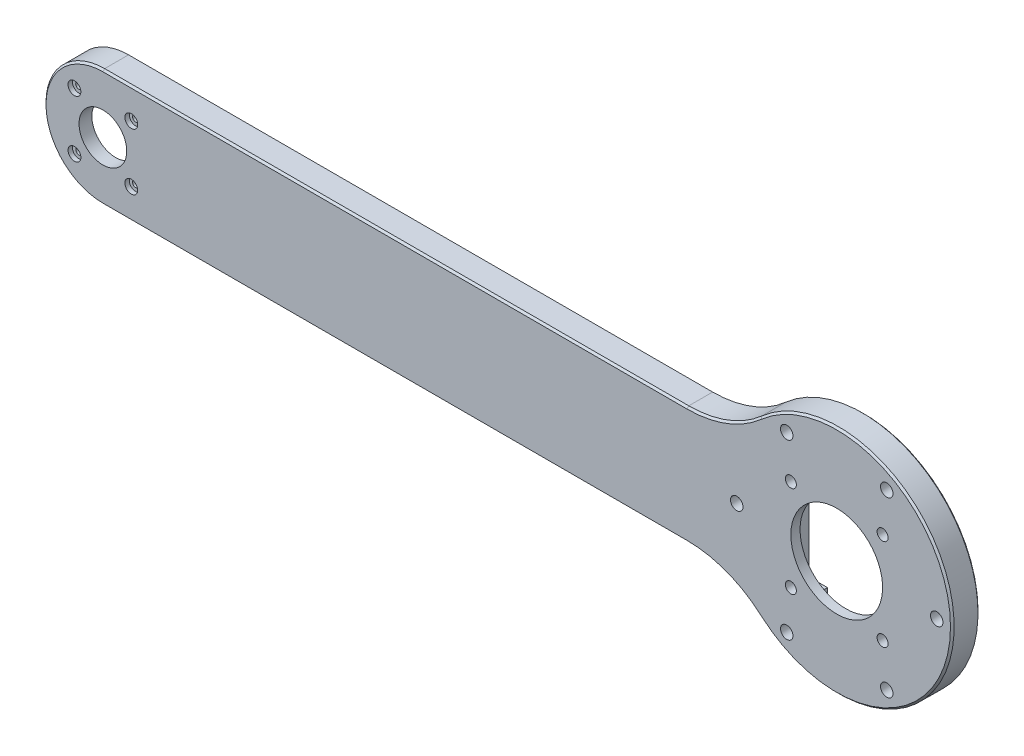
SolidWorks part; units mm, degrees
ref_plane "前基準面" through (0, 0, 0) normal (0, 0, 1) x (1, 0, 0)
ref_plane "上基準面" through (0, 0, 0) normal (0, 1, 0) x (1, 0, 0)
ref_plane "右基準面" through (0, 0, 0) normal (1, 0, 0) x (0, 0, -1)
sketch "Sketch1" plane through (0, 0, 0) normal (0, 0, 1) x (1, 0, 0)
  line L0 (393.8323, -17.9415) -> (-6.1677, -17.9415) construction
  line L1 (393.8323, 45.0585) -> (-6.1677, 45.0585)
  line L2 (393.8323, -80.9415) -> (-6.1677, -80.9415)
  line L3 (-6.1677, 14.0585) -> (339.5645, 14.0585)
  line L4 (-6.1677, -49.9415) -> (339.5645, -49.9415)
  line L6 (423.8323, -47.9415) -> (363.8323, -47.9415)
  line L7 (423.8323, -47.9415) -> (423.8323, 12.0585)
  line L8 (423.8323, 12.0585) -> (363.8323, 12.0585)
  line L9 (363.8323, -47.9415) -> (363.8323, 12.0585)
  line L10 (393.8323, 12.0585) -> (393.8323, -47.9415) construction
  line L11 (423.8323, -17.9415) -> (363.8323, -17.9415) construction
  line L12 (413.8323, -47.9415) -> (373.8323, -47.9415)
  line L13 (413.8323, -47.9415) -> (413.8323, -80.9415)
  line L14 (413.8323, -80.9415) -> (373.8323, -80.9415)
  line L15 (373.8323, -47.9415) -> (373.8323, -80.9415)
  arc A0 (393.8323, 45.0585) -> (393.8323, -80.9415) centre (393.8323, -17.9415) cw
  arc A1 (-6.1677, 45.0585) -> (-6.1677, -80.9415) centre (-6.1677, -17.9415) ccw
  circle A4 centre (-6.1677, -17.9415) radius 32
  circle A5 centre (393.8323, -17.9415) radius 63
  circle A6 centre (393.8323, -17.9415) radius 25 construction
  circle A7 centre (393.8323, -17.9415) radius 25
  arc A8 (435.6431, -47.1452) -> (352.0215, -47.1452) centre (393.8323, -17.9415) ccw construction
  dimension "D1" = 400
  dimension "D2" = 60
  dimension "D4" = 60
  dimension "D5" = 10
  dimension "D6" = 12
  dimension "D3" = 64
sketch "Sketch2" plane through (0, 0, 0) normal (0, 0, 1) x (1, 0, 0)
  line L0 (-6.1677, -49.9415) -> (339.5645, -49.9415) construction
  line L1 (-6.1677, 14.0585) -> (339.5645, 14.0585) construction
  line L2 (-6.1677, -49.9415) -> (339.5645, -49.9415)
  line L3 (-6.1677, 14.0585) -> (339.5645, 14.0585)
  circle A0 centre (-6.1677, -17.9415) radius 32 construction
  arc A2 (-6.1677, 14.0585) -> (-6.1677, -49.9415) centre (-6.1677, -17.9415) ccw
  circle A5 centre (393.8323, -17.9415) radius 63 construction
  arc A6 (339.5645, -49.9415) -> (339.5645, 14.0585) centre (393.8323, -17.9415) ccw
extrude "Boss-Extrude1" add sketch "Sketch2" along normal blind 15
fillet "Fillet1" radius 60 2 edges at (339.5645, 14.0585, 7.5) (339.5645, -49.9415, 7.5)
ref_plane "平面1" through (0, 0, 10) normal (0, 0, 1) x (1, 0, 0)
sketch "Sketch9" plane through (0, 0, 15) normal (0, 0, 1) x (1, 0, 0)
  line L0 (330.8323, -17.9415) -> (25.8323, -17.9415) construction
  line L1 (165.3718, 9.0585) -> (165.3718, -44.9415) construction
  line L2 (393.8323, -17.9415) -> (263.8323, 9.0585) construction
  line L3 (312.1929, 14.0585) -> (-6.1677, 14.0585) construction
  line L4 (336.9113, 9.0585) -> (-6.1677, 9.0585)
  line L6 (-6.1677, -44.9415) -> (312.1929, -44.9415)
  line L7 (-6.1677, -44.9415) -> (336.9113, -44.9415)
  circle A0 centre (393.8323, -17.9415) radius 63
  arc A1 (352.017, -65.0635) -> (352.017, 29.1804) centre (393.8323, -17.9415) ccw construction
  circle A2 centre (-6.1677, -17.9415) radius 32
  arc A3 (-6.1677, 14.0585) -> (-6.1677, -49.9415) centre (-6.1677, -17.9415) ccw construction
  dimension "D3" = 130
  dimension "D1" = 5
  dimension "D2" = 5
sketch "Sketch10" plane through (0, 0, 15) normal (0, 0, 1) x (1, 0, 0)
  line L0 (336.9113, 9.0585) -> (-6.1677, 9.0585) construction
  line L1 (-6.1677, -44.9415) -> (336.9113, -44.9415) construction
  line L2 (336.9113, 9.0585) -> (11.0079, 9.0585)
  line L3 (11.0079, -44.9415) -> (336.9113, -44.9415)
  circle A0 centre (393.8323, -17.9415) radius 63 construction
  circle A1 centre (-6.1677, -17.9415) radius 32 construction
  arc A2 (336.9113, 9.0585) -> (336.9113, -44.9415) centre (393.8323, -17.9415) ccw
  arc A3 (11.0079, -44.9415) -> (11.0079, 9.0585) centre (-6.1677, -17.9415) ccw
extrude "Cut-Extrude4" [suppressed] cut sketch "Sketch10" against normal offset from surface (12 mm away) 3
sketch "草圖2" plane through (0, 0, 0) normal (0, 0, -1) x (-1, 0, 0)
  circle A0 centre (-393.8323, -17.9415) radius 25 construction
  circle A1 centre (-393.8323, -17.9415) radius 25
extrude "除料-伸長2" cut sketch "草圖2" against normal through all
sketch "草圖1" plane through (0, 0, 0) normal (0, 0, -1) x (-1, 0, 0)
  line L0 (-423.8323, 12.0585) -> (-363.8323, 12.0585) construction
  line L1 (-363.8323, -47.9415) -> (-363.8323, 12.0585) construction
  line L2 (-423.8323, -47.9415) -> (-363.8323, -47.9415) construction
  line L3 (-423.8323, -47.9415) -> (-423.8323, 12.0585) construction
  line L4 (-423.8323, 12.0585) -> (-363.8323, 12.0585)
  line L5 (-363.8323, -47.9415) -> (-363.8323, 12.0585)
  line L6 (-423.8323, -47.9415) -> (-363.8323, -47.9415)
  line L7 (-423.8323, -47.9415) -> (-423.8323, 12.0585)
extrude "除料-伸長1" cut sketch "草圖1" against normal up to surface (10 mm away)
sketch "草圖3" plane through (0, 0, 0) normal (0, 0, -1) x (-1, 0, 0)
  line L0 (-373.8323, -47.9415) -> (-373.8323, -80.9415) construction
  line L1 (-413.8323, -80.9415) -> (-373.8323, -80.9415) construction
  line L2 (-413.8323, -47.9415) -> (-413.8323, -80.9415) construction
  line L3 (-413.8323, -47.9415) -> (-373.8323, -47.9415) construction
  line L4 (-373.8323, -47.9415) -> (-373.8323, -80.9415)
  line L5 (-413.8323, -80.9415) -> (-373.8323, -80.9415)
  line L6 (-413.8323, -47.9415) -> (-413.8323, -80.9415)
  line L7 (-413.8323, -47.9415) -> (-373.8323, -47.9415)
extrude "除料-伸長3" cut sketch "草圖3" against normal offset from surface (7 mm away) 3 up to plane "平面1"
hole_wizard "M7x1.0 螺紋孔1" positions "草圖6" profile "草圖5" tap size "M7x1.0" standard "JIS"
sketch "草圖6" plane through (0, 0, 10) normal (0, 0, -1) x (-1, 0, 0)
  point P0 (-368.8323, 7.0585)
  point P3 (-368.8323, -42.9415)
  point P6 (-418.8323, -42.9415)
  point P9 (-418.8323, 7.0585)
sketch "草圖5" plane through (368.8323, 7.0585, 10) normal (1, 0, 0) x (0, 1, 0)
  line L0 (0, 0) -> (0, 18.8026)
  line L1 (0, 18.8026) -> (3, 17)
  line L2 (3, 17) -> (3, 0)
  line L5 (3, 0) -> (0, 0)
  line L10 (0, 18.8026) -> (-3, 17) construction
  line L11 (0, -6.35) -> (0, 107.95) construction
  dimension "螺孔鑽直徑" = 6
  dimension "螺孔鑽深度" = 17
  dimension "導頭角度" = 118
cosmetic thread "鑽孔螺紋1" parameters "D1"=14, "D2"=7
cosmetic thread "鑽孔螺紋2" parameters "D1"=14, "D2"=7
cosmetic thread "鑽孔螺紋3" parameters "D1"=14, "D2"=7
cosmetic thread "鑽孔螺紋4" parameters "D1"=14, "D2"=7
hole_wizard "M8x1.25 螺紋孔1" positions "草圖9" profile "草圖8" tap size "M8x1.25" standard "JIS"
sketch "草圖9" plane through (0, 0, 15) normal (0, 0, 1) x (1, 0, 0)
  arc A3 (352.017, -65.0635) -> (352.017, 29.1804) centre (393.8323, -17.9415) ccw construction
  point P1 (448.3323, -17.9415)
  point P24 (456.8323, -17.9415)
  dimension "D1" = 8.5
sketch "草圖8" plane through (448.3323, -17.9415, 15) normal (1, 0, 0) x (0, -1, 0)
  line L0 (0, 0) -> (0, 21.7929)
  line L1 (0, 21.7929) -> (3.4, 19.75)
  line L2 (3.4, 19.75) -> (3.4, 0)
  line L5 (3.4, 0) -> (0, 0)
  line L10 (0, 21.7929) -> (-3.4, 19.75) construction
  line L11 (0, -6.35) -> (0, 107.95) construction
  dimension "螺孔鑽直徑" = 6.8
  dimension "螺孔鑽深度" = 19.75
  dimension "導頭角度" = 118
cosmetic thread "鑽孔螺紋5" parameters "D1"=16, "D2"=8
pattern_circular "環狀複製排列1" count 6 every 60 about axis through (393.8323, -17.9415, 0) along (0, 0, 1) of "M8x1.25 螺紋孔1"
cosmetic thread "鑽孔螺紋6" parameters "D1"=16, "D2"=8
cosmetic thread "鑽孔螺紋7" parameters "D1"=16, "D2"=8
cosmetic thread "鑽孔螺紋8" parameters "D1"=16, "D2"=8
cosmetic thread "鑽孔螺紋9" parameters "D1"=16, "D2"=8
cosmetic thread "鑽孔螺紋10" parameters "D1"=16, "D2"=8
sketch "Sketch3" plane through (0, 0, 15) normal (0, 0, 1) x (1, 0, 0)
  line L1 (-27.1677, 3.0585) -> (14.8323, 3.0585)
  line L2 (-27.1677, 3.0585) -> (-27.1677, -38.9415)
  line L3 (-27.1677, -38.9415) -> (14.8323, -38.9415)
  line L4 (14.8323, 3.0585) -> (14.8323, -38.9415)
  line L5 (-6.1677, -38.9415) -> (-6.1677, 3.0585) construction
  line L6 (-27.1677, -17.9415) -> (14.8323, -17.9415) construction
  circle A0 centre (-6.1677, -17.9415) radius 13
  arc A1 (6.0716, 3.0585) -> (-18.407, 3.0585) centre (-6.1677, -4.1415) cw construction
  arc A3 (6.0716, 3.0585) -> (-18.407, 3.0585) centre (-6.1677, -4.1415) ccw construction
  arc A4 (-19.5543, 3.0585) -> (7.2189, 3.0585) centre (-6.1677, -4.1415) cw
  arc A5 (6.9335, 3.5655) -> (-19.2689, 3.5655) centre (-6.1677, -4.1415) cw construction
  point P0 (-6.1677, -17.9415)
  dimension "D3" = 26
  dimension "D1" = 42
  dimension "D2" = 42
  dimension "D4" = 1
sketch "Sketch5" plane through (0, 0, 15) normal (0, 0, 1) x (1, 0, 0)
  circle A0 centre (-6.1677, -17.9415) radius 13 construction
  circle A1 centre (-6.1677, -17.9415) radius 13
extrude "Cut-Extrude2" cut sketch "Sketch5" against normal through all
sketch "Sketch4" plane through (0, 0, 15) normal (0, 0, 1) x (1, 0, 0)
  line L0 (-27.1677, 3.0585) -> (14.8323, 3.0585) construction
  line L1 (-27.1677, -38.9415) -> (14.8323, -38.9415) construction
  line L2 (-27.1677, 3.0585) -> (-27.1677, -38.9415) construction
  line L3 (14.8323, 3.0585) -> (14.8323, -38.9415) construction
  line L4 (-27.1677, 3.0585) -> (14.8323, 3.0585)
  line L5 (-27.1677, -38.9415) -> (14.8323, -38.9415)
  line L6 (-27.1677, 3.0585) -> (-27.1677, -38.9415)
  line L7 (14.8323, 3.0585) -> (14.8323, -38.9415)
  point P0 (0, 0)
extrude "Cut-Extrude1" cut sketch "Sketch4" along normal offset from surface (8 mm away) 7 from surface at -15 up to face at (6.8323, -17.9415, 15) starting at face at (6.8323, -17.9415, 0)
sketch "Sketch8" plane through (0, 0, 15) normal (0, 0, 1) x (1, 0, 0)
  line L0 (-27.1677, 3.0585) -> (14.8323, 3.0585) construction
  line L1 (-19.5543, 3.0585) -> (7.2189, 3.0585)
  arc A0 (7.2189, 3.0585) -> (-19.5543, 3.0585) centre (-6.1677, -4.1415) ccw construction
  arc A1 (7.2189, 3.0585) -> (-19.5543, 3.0585) centre (-6.1677, -4.1415) ccw
extrude "Cut-Extrude3" cut sketch "Sketch8" along normal up to surface (8 mm away) from surface at -15 up to face at (-6.1677, -17.9415, 8) starting at face at (321.5943, -28.1365, 0)
fillet "Fillet2" radius 3 6 edges at (-27.1677, -38.9415, 4) (14.8323, -38.9415, 4) (14.8323, 3.0585, 4) (-27.1677, 3.0585, 4) (-19.5543, 3.0585, 4) (7.2189, 3.0585, 4)
chamfer "Chamfer1" distance 1 angle 45 13 edges at (333.4921, -53.8492, 15) (456.8323, -17.9415, 15) (153.0126, -49.9415, 15) (333.4921, 17.9662, 15) (-38.1677, -17.9415, 15) (153.0126, 14.0585, 15) (362.2872, -72.475, 0) (333.4921, -53.8492, 0) (448.3658, 13.6036, 0) (153.0126, -49.9415, 0) (333.4921, 17.9662, 0) (-38.1677, -17.9415, 0) (153.0126, 14.0585, 0)
hole_wizard "CBORE for M3 Pan Head Screw1" positions "Sketch6" profile "Sketch7" counterbore size "M3" standard "JIS" end condition through all
sketch "Sketch6" plane through (0, 0, 15) normal (0, 0, -1) x (-1, 0, 0)
  point P0 (21.6677, -2.4415)
  point P3 (21.6533, -33.4271)
  point P6 (-9.3179, -33.4271)
  point P9 (-9.3323, -2.4415)
sketch "Sketch7" plane through (-21.6677, -2.4415, 15) normal (1, 0, 0) x (0, -1, 0)
  line L0 (0, 0) -> (0, 15)
  line L1 (0, 15) -> (1.7, 15)
  line L3 (1.7, 15) -> (1.7, 2.4)
  line L4 (1.7, 2.4) -> (3.5, 2.4)
  line L5 (3.5, 2.4) -> (3.5, 0)
  line L7 (3.5, 0) -> (0, 0)
  line L11 (0, -6.35) -> (0, 107.95) construction
  dimension "Thru Hole Dia." = 3.4
  dimension "Thru Hole Depth" = 15
  dimension "C'Bore Dia." = 7
  dimension "C'Bore Depth" = 2.4
sketch "Sketch11" [suppressed] plane through (0, 0, 15) normal (0, 0, 1) x (1, 0, 0)
  line L1 (393.8323, -17.9415) -> (263.8323, 9.0585) construction
  line L2 (334.1069, -5.537) -> (263.8323, 9.0585)
  circle A0 centre (393.8323, -17.9415) radius 61 construction
  circle A1 centre (393.8323, -17.9415) radius 61 construction
rib "Rib7" [suppressed] sketch "Sketch11" sketch "Sketch11" thickness 5 extrusion direction normal to sketch draft on no parameters "D1"=5
sketch "Sketch12" [suppressed] plane through (0, 0, 15) normal (0, 0, 1) x (1, 0, 0)
  line L0 (332.8323, -17.9415) -> (25.8323, -17.9415)
rib "Rib8" [suppressed] sketch "Sketch12" sketch "Sketch12" thickness 5 extrusion direction normal to sketch draft on no parameters "D1"=5
ref_plane "Plane1" [suppressed] through (166.4827, 0, 0) normal (1, 0, 0) x (0, 0, -1)
ref_plane "Plane2" [suppressed] through (0, -17.9415, 0) normal (0, -1, 0) x (-1, 0, 0)
mirror "Mirror3" [suppressed] about plane through (0, -17.9415, 0) normal (0, -1, 0)
mirror "Mirror4" [suppressed] about plane through (166.4827, 0, 0) normal (1, 0, 0)
fillet "Fillet5" [suppressed] radius 60
fillet "Fillet4" [suppressed] radius 3
fillet "Fillet3" [suppressed] radius 1
fillet "Fillet6" radius 4 4 edges at (363.8323, 12.0585, 5) (363.8323, -47.9415, 5) (423.8323, -47.9415, 5) (423.8323, 12.0585, 5)
equation "\"D1@Boss-Extrude1\" = \"thick@零件5-1<1>.Part\""
equation "\"D1@Sketch1\"=\"Lenth_ArmB@組合件1.Assembly\""
equation "\"Rib_thick\"= 5"
equation "\"D1@Rib7\"=\"Rib_thick\""
equation "\"D1@Rib8\"=\"Rib_thick\""
equation "\"D2@Sketch9\"=\"Rib_thick\""
equation "\"D1@Sketch9\"=\"D2@Sketch9\""
